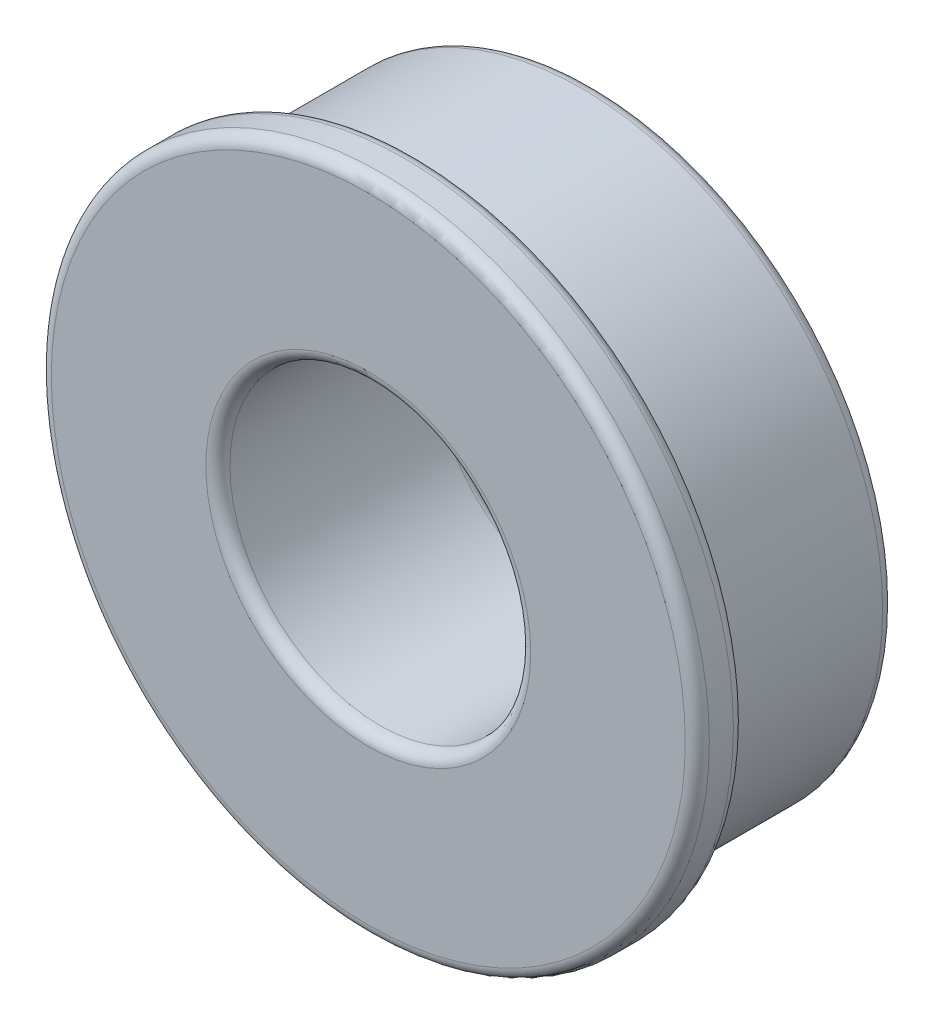
SolidWorks part; units mm, degrees
ref_plane "Front Plane" through (0, 0, 0) normal (0, 0, 1) x (1, 0, 0)
ref_plane "Top Plane" through (0, 0, 0) normal (0, 1, 0) x (1, 0, 0)
ref_plane "Right Plane" through (0, 0, 0) normal (1, 0, 0) x (0, 0, -1)
sketch "Sketch1" plane through (0, 0, 0) normal (0, 0, 1) x (1, 0, 0)
  circle A0 centre (0, 0) radius 6.35
  dimension "D1" = 12.7
extrude "Boss-Extrude1" add sketch "Sketch1" along normal blind 4.7625
sketch "Sketch2" plane through (0, 0, 4.7625) normal (0, 0, 1) x (1, 0, 0)
  circle A0 centre (0, 0) radius 6.9453
  dimension "D1" = 13.8906
extrude "Boss-Extrude2" add sketch "Sketch2" against normal blind 1.016
sketch "Sketch3" plane through (0, 0, 4.7625) normal (0, 0, 1) x (1, 0, 0)
  circle A0 centre (0, 0) radius 3.175
  dimension "D1" = 6.35
extrude "Cut-Extrude1" cut sketch "Sketch3" against normal up to surface (4.7625 mm away) up to face at (6.35, 0, 0)
fillet "Fillet1" radius 0.254 6 edges at (6.35, 0, 3.7465) (6.35, 0, 0) (3.175, 0, 0) (6.9453, 0, 3.7465) (6.9453, 0, 4.7625) (3.175, 0, 4.7625)
